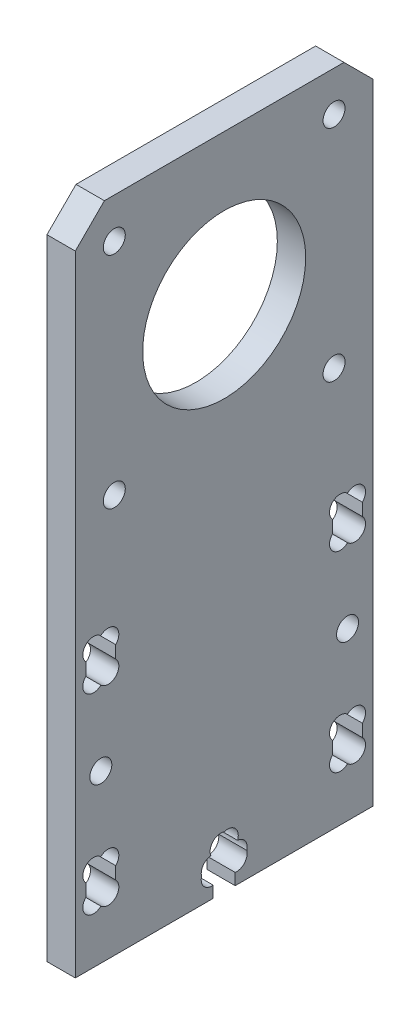
SolidWorks part; units mm, degrees
ref_plane "Alzado" through (0, 0, 0) normal (0, 0, 1) x (1, 0, 0)
ref_plane "Planta" through (0, 0, 0) normal (0, 1, 0) x (1, 0, 0)
ref_plane "Vista lateral" through (0, 0, 0) normal (1, 0, 0) x (0, 0, -1)
sketch "Croquis1" plane through (0, 0, 0) normal (1, 0, 0) x (0, 0, -1)
  line L0 (5.5, 87.26) -> (36.5, 56.26) construction
  line L1 (0, 0) -> (42, 0)
  line L2 (0, 0) -> (0, 92.91)
  line L3 (0, 92.91) -> (42, 92.91)
  line L4 (42, 0) -> (42, 92.91)
  line L5 (5.5, 56.26) -> (36.5, 87.26) construction
  line L6 (21, 71.76) -> (21, 92.91) construction
  circle A0 centre (21, 71.76) radius 11.5
  circle A1 centre (5.5, 87.26) radius 1.55
  circle A2 centre (36.5, 87.26) radius 1.55
  circle A3 centre (36.5, 56.26) radius 1.55
  circle A4 centre (5.5, 56.26) radius 1.55
  dimension "D3" = 23
  dimension "D4" = 3.1
  dimension "D1" = 31
  dimension "D2" = 31
  dimension "D5" = 42
  dimension "D6" = 21.15
  dimension "D7" = 71.76
extrude "Saliente-Extruir1" add sketch "Croquis1" along normal blind 4
sketch "Croquis2" plane through (4, 0, 0) normal (1, 0, 0) x (0, 0, -1)
  line L0 (21, 0) -> (21, 54.7908) construction
  line L1 (1.5, 40) -> (5.7, 40)
  line L2 (1.5, 40) -> (1.5, 34)
  line L3 (1.5, 34) -> (5.7, 34)
  line L4 (5.7, 40) -> (5.7, 34)
  line L5 (1.5, 13) -> (5.7, 13)
  line L6 (1.5, 13) -> (1.5, 7)
  line L7 (1.5, 7) -> (5.7, 7)
  line L8 (5.7, 13) -> (5.7, 7)
  line L9 (38.4, 34) -> (38.4, 13) construction
  line L10 (36.3, 13) -> (36.3, 7)
  line L11 (40.5, 7) -> (36.3, 7)
  line L12 (40.5, 13) -> (40.5, 7)
  line L13 (40.5, 13) -> (36.3, 13)
  line L14 (36.3, 40) -> (36.3, 34)
  line L15 (40.5, 34) -> (36.3, 34)
  line L16 (40.5, 40) -> (40.5, 34)
  line L17 (40.5, 40) -> (36.3, 40)
  line L25 (0, 0) -> (42, 0) construction
  line L26 (3.6, 34) -> (3.6, 13) construction
  line L27 (0, 92.91) -> (0, 0) construction
  circle A0 centre (3.6, 23.5) radius 1.55
  circle A1 centre (38.4, 23.5) radius 1.55
  dimension "D3" = 3.1
  dimension "D1" = 4.2
  dimension "D2" = 6
  dimension "D4" = 40
  dimension "D5" = 1.5
  dimension "D6" = 7
extrude "Cortar-Extruir1" cut sketch "Croquis2" against normal through all
sketch "Croquis3" plane through (4, 0, 0) normal (1, 0, 0) x (0, 0, -1)
  line L0 (19.45, 0) -> (19.45, 2.05)
  line L1 (0, 0) -> (42, 0) construction
  line L2 (19.45, 2.05) -> (18.2, 2.05)
  line L3 (18.2, 2.05) -> (18.2, 4.95)
  line L4 (18.2, 4.95) -> (19.45, 4.95)
  line L5 (23.8, 4.95) -> (23.8, 2.05)
  line L6 (23.8, 2.05) -> (22.55, 2.05)
  line L7 (22.55, 2.05) -> (22.55, 0)
  line L8 (22.55, 0) -> (19.45, 0)
  line L9 (21, 7) -> (21, 92.91) construction
  line L10 (19.45, 4.95) -> (19.45, 7)
  line L11 (19.45, 7) -> (22.55, 7)
  line L12 (22.55, 7) -> (22.55, 4.95)
  line L13 (22.55, 4.95) -> (23.8, 4.95)
  line L14 (42, 92.91) -> (0, 92.91) construction
  line L15 (18.2, 3.5) -> (23.8, 3.5) construction
  dimension "D1" = 3.1
  dimension "D2" = 2.9
  dimension "D3" = 5.6
  dimension "D4" = 7
  dimension "D5" = 3.5
extrude "Cortar-Extruir2" cut sketch "Croquis3" against normal through all
sketch "Croquis4" plane through (4, 0, 0) normal (1, 0, 0) x (0, 0, -1)
  line L0 (5.7, 40) -> (1.5, 40) construction
  line L1 (1.5, 40) -> (1.5, 34) construction
  line L2 (1.5, 40) -> (3, 38.5) construction
  line L3 (1.5, 37) -> (5.7, 37) construction
  line L4 (5.7, 34) -> (5.7, 40) construction
  line L6 (3.6, 40) -> (3.6, 34) construction
  line L7 (1.5, 34) -> (5.7, 34) construction
  line L8 (5.7, 37.8787) -> (5.7, 36.1213)
  line L10 (1.5, 36.1213) -> (1.5, 37.8787)
  line L11 (3.6, 23.5) -> (38.4, 23.5) construction
  line L12 (21, 92.91) -> (21, 23.5) construction
  line L13 (42, 92.91) -> (0, 92.91) construction
  line L14 (40.5, 36.1213) -> (40.5, 37.8787)
  line L16 (36.3, 37.8787) -> (36.3, 36.1213)
  line L19 (36.3, 9.1213) -> (36.3, 10.8787)
  line L21 (40.5, 10.8787) -> (40.5, 9.1213)
  line L22 (5.7, 9.1213) -> (5.7, 10.8787)
  line L24 (1.5, 10.8787) -> (1.5, 9.1213)
  circle A0 centre (3, 38.5) radius 1.5 construction
  arc A1 (3.6, 40.0209) -> (1.5, 37.8787) centre (2.5607, 38.9393) ccw
  arc A2 (3.6, 33.9791) -> (1.5, 36.1213) centre (2.5607, 35.0607) cw
  arc A3 (3.6, 33.9791) -> (5.7, 36.1213) centre (4.6393, 35.0607) ccw
  arc A4 (3.6, 40.0209) -> (5.7, 37.8787) centre (4.6393, 38.9393) cw
  arc A5 (38.4, 33.9791) -> (40.5, 36.1213) centre (39.4393, 35.0607) ccw
  arc A6 (38.4, 33.9791) -> (36.3, 36.1213) centre (37.3607, 35.0607) cw
  arc A7 (38.4, 40.0209) -> (36.3, 37.8787) centre (37.3607, 38.9393) ccw
  arc A8 (38.4, 40.0209) -> (40.5, 37.8787) centre (39.4393, 38.9393) cw
  arc A9 (38.4, 6.9791) -> (40.5, 9.1213) centre (39.4393, 8.0607) ccw
  arc A10 (38.4, 6.9791) -> (36.3, 9.1213) centre (37.3607, 8.0607) cw
  arc A11 (38.4, 13.0209) -> (36.3, 10.8787) centre (37.3607, 11.9393) ccw
  arc A12 (38.4, 13.0209) -> (40.5, 10.8787) centre (39.4393, 11.9393) cw
  arc A13 (3.6, 13.0209) -> (5.7, 10.8787) centre (4.6393, 11.9393) cw
  arc A14 (3.6, 13.0209) -> (1.5, 10.8787) centre (2.5607, 11.9393) ccw
  arc A15 (3.6, 6.9791) -> (5.7, 9.1213) centre (4.6393, 8.0607) ccw
  arc A16 (3.6, 6.9791) -> (1.5, 9.1213) centre (2.5607, 8.0607) cw
  dimension "D1" = 3
extrude "Cortar-Extruir3" cut sketch "Croquis4" against normal through all
sketch "Croquis5" plane through (4, 0, 0) normal (1, 0, 0) x (0, 0, -1)
  line L0 (22.55, 7) -> (19.45, 7) construction
  line L2 (19.45, 7) -> (19.45, 4.95) construction
  line L3 (19.45, 4.95) -> (18.2, 4.95) construction
  line L4 (18.2, 4.95) -> (18.2, 2.05) construction
  line L5 (18.2, 2.05) -> (19.45, 2.05) construction
  line L6 (19.45, 7) -> (20.95, 5.5) construction
  line L7 (19.7, 3.55) -> (18.2, 2.05) construction
  line L8 (19.7, 3.45) -> (18.2, 4.95) construction
  line L9 (21, 7) -> (21, -0.5578) construction
  line L18 (21.6787, 2.05) -> (20.3213, 2.05)
  circle A0 centre (20.95, 5.5) radius 1.5 construction
  circle A1 centre (19.7, 3.45) radius 1.5 construction
  circle A2 centre (19.7, 3.55) radius 1.5 construction
  arc A3 (21, 7.3573) -> (19.1178, 5.3825) centre (20.5107, 5.9393) ccw
  arc A5 (17.8121, 3.5) -> (20.3213, 2.05) centre (19.2607, 3.1107) ccw
  arc A6 (24.1879, 3.5) -> (21.6787, 2.05) centre (22.7393, 3.1107) cw
  arc A7 (22.8822, 5.3825) -> (24.1879, 3.5) centre (22.7393, 3.8893) cw
  arc A8 (21, 7.3573) -> (22.8822, 5.3825) centre (21.4893, 5.9393) cw
  arc A10 (19.1178, 5.3825) -> (17.8121, 3.5) centre (19.2607, 3.8893) ccw
  dimension "D1" = 3
extrude "Cortar-Extruir4" cut sketch "Croquis5" against normal through all
chamfer "Chaflán1" distance 4.1 angle 45 2 edges at (2, 92.91, -42) (2, 92.91, 0)
